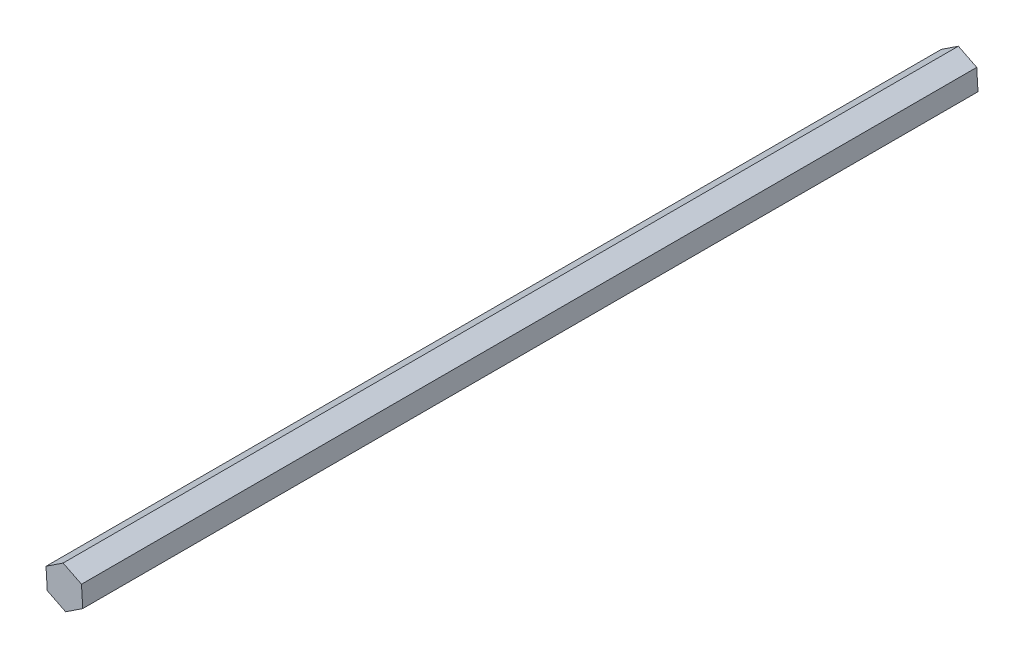
SolidWorks part; units mm, degrees
ref_plane "Front Plane" through (0, 0, 0) normal (0, 0, 1) x (1, 0, 0)
ref_plane "Top Plane" through (0, 0, 0) normal (0, 1, 0) x (1, 0, 0)
ref_plane "Right Plane" through (0, 0, 0) normal (1, 0, 0) x (0, 0, -1)
sketch "Sketch1" plane through (0, 0, 0) normal (0, 0, 1) x (1, 0, 0)
  line L1 (-0.4538, 7.336) -> (-6.58, 3.275)
  line L2 (-6.58, 3.275) -> (-6.1263, -4.061)
  line L3 (-6.1263, -4.061) -> (0.4538, -7.336)
  line L4 (0.4538, -7.336) -> (6.58, -3.275)
  line L5 (6.58, -3.275) -> (6.1263, 4.061)
  line L6 (6.1263, 4.061) -> (-0.4538, 7.336)
  circle A0 centre (0, 0) radius 6.3653 construction
  dimension "D1" = 7.35
extrude "Boss-Extrude1" add sketch "Sketch1" along normal blind 320.55
